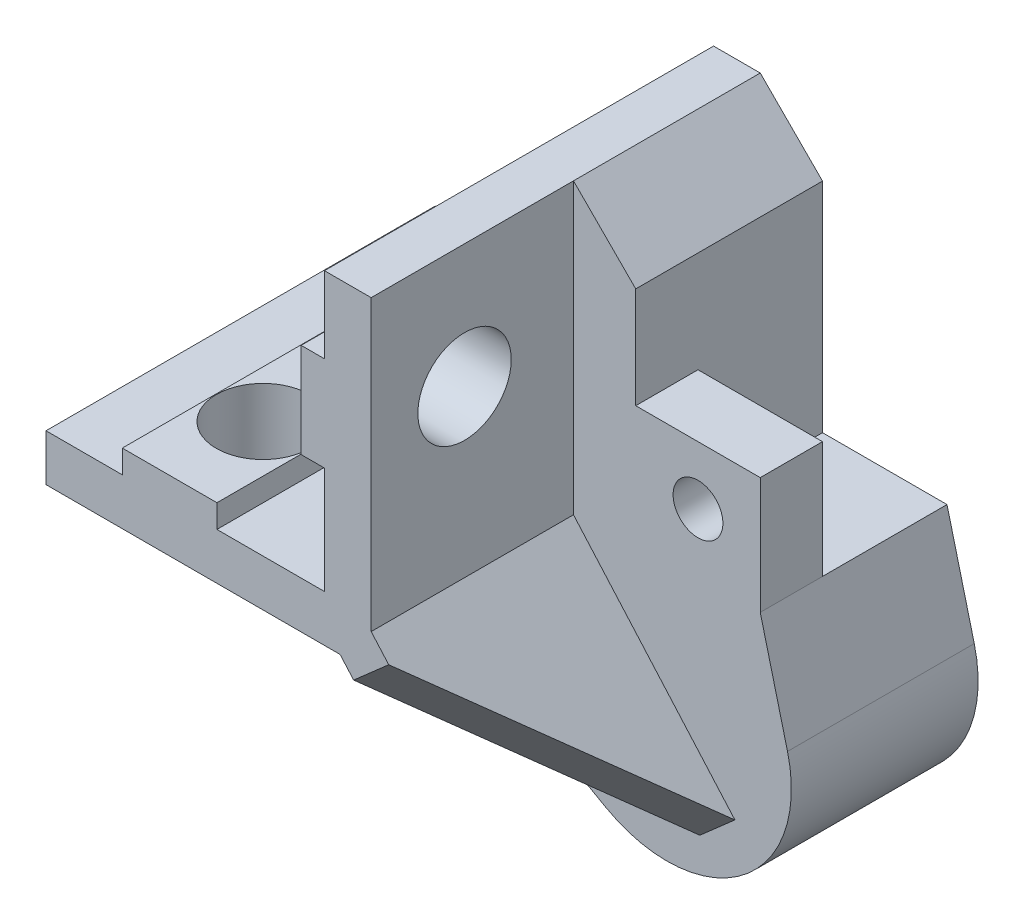
SolidWorks part; units mm, degrees
material "ABS"
ref_plane "Front Plane" through (0, 0, 0) normal (0, 0, 1) x (1, 0, 0)
ref_plane "Top Plane" through (0, 0, 0) normal (0, 1, 0) x (1, 0, 0)
ref_plane "Right Plane" through (0, 0, 0) normal (1, 0, 0) x (0, 0, -1)
sketch "Sketch1" plane through (0, 0, 0) normal (0, 0, 1) x (1, 0, 0)
  line L0 (227.0887, 62.283) -> (227.0887, 57.3796)
  line L1 (227.0887, 44.4296) -> (220.1787, 44.4296)
  line L2 (209.1953, 44.4296) -> (209.1953, 41.4296)
  line L3 (209.1953, 41.4296) -> (230.0887, 41.4296)
  line L4 (230.0887, 41.4296) -> (230.0887, 62.283)
  line L5 (230.0887, 62.283) -> (227.0887, 62.283)
  line L6 (214.0987, 45.9172) -> (214.0987, 44.4296)
  line L7 (220.1787, 45.9172) -> (220.1787, 44.4296)
  line L8 (220.1787, 45.9172) -> (214.0987, 45.9172)
  line L9 (225.5901, 57.3796) -> (227.0887, 57.3796)
  line L10 (225.5901, 51.2996) -> (227.0887, 51.2996)
  line L11 (225.5901, 51.2996) -> (225.5901, 57.3796)
  line L12 (227.0887, 51.2996) -> (227.0887, 44.4296)
  line L13 (214.0987, 44.4296) -> (209.1953, 44.4296)
  dimension "D1" = 17.8534
  dimension "D2" = 17.8934
  dimension "D3" = 1.4876
  dimension "D4" = 4.9034
  dimension "D5" = 4.9034
  dimension "D6" = 6.08
  dimension "D7" = 1.4986
  dimension "D8" = 3
extrude "Boss-Extrude1" add sketch "Sketch1" against normal blind 25
sketch3d "3DSketch1"
  line L0 (225.5901, 54.3396, 0) -> (230.0887, 54.3396, 0) construction
  line L1 (225.5901, 57.3796, 0) -> (225.5901, 51.2996, 0) construction
  line L2 (230.0887, 41.4296, 0) -> (230.0887, 62.283, 0) construction
  line L3 (230.0887, 54.3396, 0) -> (230.0887, 54.3396, -25) construction
  line L4 (230.0887, 41.4296, -25) -> (230.0887, 62.283, -25) construction
  line L5 (217.1387, 45.9172, 0) -> (217.1387, 41.4296, 0) construction
  line L6 (220.1787, 45.9172, 0) -> (214.0987, 45.9172, 0) construction
  line L7 (209.1953, 41.4296, 0) -> (230.0887, 41.4296, 0) construction
  line L8 (217.1387, 41.4296, 0) -> (217.1387, 41.4296, -25) construction
  line L9 (209.1953, 41.4296, -25) -> (230.0887, 41.4296, -25) construction
sketch "Sketch2" plane through (230.0887, 0, 0) normal (1, 0, 0) x (0, 0, -1)
  circle A0 centre (6, 54.3396) radius 3
  dimension "D1" = 6
  dimension "D2" = 6
extrude "Cut-Extrude1" cut sketch "Sketch2" against normal blind 15
sketch "Sketch3" plane through (0, 41.4296, 0) normal (0, -1, 0) x (1, 0, 0)
  circle A0 centre (217.1387, -6) radius 3
  dimension "D1" = 6
  dimension "D2" = 6
extrude "Cut-Extrude2" cut sketch "Sketch3" against normal blind 15
sketch "Sketch4" plane through (0, 0, -25) normal (0, 0, -1) x (-1, 0, 0)
  line L0 (-230.0887, 62.283) -> (-234.0887, 58.2696)
  line L1 (-230.0887, 62.283) -> (-227.0887, 62.283) construction
  line L2 (-232.1548, 28.4636) -> (-209.1953, 41.4296)
  line L3 (-209.1953, 41.4296) -> (-230.0887, 41.4296) construction
  line L4 (-209.1953, 44.4296) -> (-209.1953, 41.4296) construction
  line L5 (-209.1953, 41.4296) -> (-230.0887, 41.4296)
  line L6 (-230.0887, 41.4296) -> (-230.0887, 62.283)
  line L7 (-234.0887, 58.2696) -> (-234.0887, 44.2696)
  line L8 (-234.0887, 44.2696) -> (-242.0887, 44.2696)
  line L9 (-242.0887, 44.2696) -> (-243.8402, 37.4082)
  arc A0 (-243.8402, 37.4082) -> (-232.1548, 28.4636) centre (-236.0887, 35.4296) ccw
  dimension "D3" = 8
  dimension "D1" = 6
  dimension "D2" = 6
extrude "Boss-Extrude2" add sketch "Sketch4" against normal blind 12
ref_plane "Plane1" through (150.2958, 132.1672, 0) normal (-0.7509, -0.6604, 0) x (0.6604, -0.7509, 0)
sketch "Sketch5" plane through (150.2958, 132.1672, 0) normal (-0.7509, -0.6604, 0) x (0.6604, -0.7509, 0)
  line L1 (120.8314, -13) -> (120.8314, 0) construction
  line L2 (120.8314, -13) -> (134.8314, -13)
  line L3 (134.8314, -13) -> (120.8314, 0)
  line L4 (120.8314, 0) -> (116.5975, 0)
  line L5 (116.5975, 0) -> (116.5975, -13)
  line L6 (116.5975, -13) -> (120.8314, -13)
  dimension "D1" = 14
extrude "Boss-Extrude4" add sketch "Sketch5" along normal mid plane 3
sketch "Sketch6" plane through (0, 0, -25) normal (0, 0, -1) x (-1, 0, 0)
  circle A1 centre (-236.0887, 35.4296) radius 4.85
  arc A2 (-243.8402, 37.4082) -> (-232.1548, 28.4636) centre (-236.0887, 35.4296) ccw construction
  dimension "D1" = 9.7
extrude "Cut-Extrude3" cut sketch "Sketch6" against normal blind 9
sketch "Sketch7" plane through (0, 0, -13) normal (0, 0, 1) x (1, 0, 0)
  line L1 (242.0887, 44.2696) -> (234.0887, 44.2696)
  line L2 (242.0887, 44.2696) -> (242.0887, 51.7696)
  line L3 (242.0887, 51.7696) -> (234.0887, 51.7696)
  line L4 (234.0887, 44.2696) -> (234.0887, 51.7696)
  dimension "D1" = 7.5
  dimension "D2" = 8
extrude "Boss-Extrude5" add sketch "Sketch7" against normal blind 4
sketch "Sketch8" plane through (0, 0, -13) normal (0, 0, 1) x (1, 0, 0)
  line L0 (242.0887, 48.0196) -> (238.0887, 48.0196) construction
  line L1 (242.0887, 44.2696) -> (242.0887, 51.7696) construction
  line L2 (238.0887, 48.0196) -> (238.0887, 51.7696) construction
  line L3 (242.0887, 51.7696) -> (234.0887, 51.7696) construction
  circle A0 centre (238.0887, 48.0196) radius 1.6
  dimension "D1" = 3.2
extrude "Cut-Extrude4" cut sketch "Sketch8" against normal blind 4
